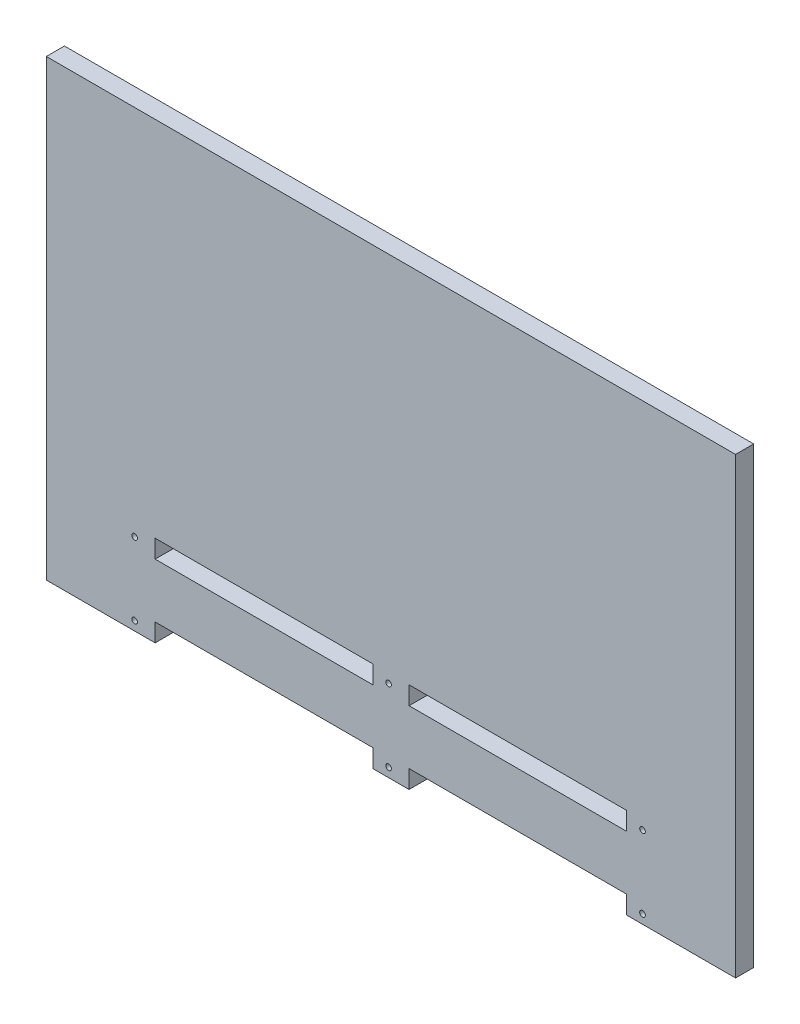
SolidWorks part; units mm, degrees
ref_plane "Ön Düzlem" through (0, 0, 0) normal (0, 0, 1) x (1, 0, 0)
ref_plane "Üst Düzlem" through (0, 0, 0) normal (0, 1, 0) x (1, 0, 0)
ref_plane "Sağ Düzlem" through (0, 0, 0) normal (1, 0, 0) x (0, 0, -1)
sketch "Çizim1" plane through (0, 0, 0) normal (0, 0, 1) x (1, 0, 0)
  line L0 (-130, -250) -> (-10, -250)
  line L1 (-150, -250) -> (150, -250)
  line L2 (-150, -250) -> (-150, 250)
  line L3 (-150, 250) -> (150, 250)
  line L4 (150, -250) -> (150, 250)
  line L5 (-150, -250) -> (150, 250) construction
  line L6 (-150, 250) -> (150, -250) construction
  line L7 (-130, -250) -> (-130, -240)
  line L8 (-10, -250) -> (-10, -240)
  line L9 (-130, -240) -> (-10, -240)
  line L10 (10, -250) -> (130, -250)
  line L11 (10, -250) -> (10, -240)
  line L12 (130, -250) -> (130, -240)
  line L13 (10, -240) -> (130, -240)
  line L14 (-130, -200) -> (-10, -200)
  line L15 (-130, -200) -> (-130, -210)
  line L16 (-10, -200) -> (-10, -210)
  line L17 (-130, -210) -> (-10, -210)
  line L18 (10, -200) -> (10, -210)
  line L19 (10, -200) -> (130, -200)
  line L20 (10, -210) -> (130, -210)
  line L21 (130, -200) -> (130, -210)
  line L22 (190, 0) -> (-190, 0)
  line L23 (-150, -250) -> (-190, -250)
  line L24 (-150, -250) -> (-150, 250)
  line L25 (-150, 250) -> (-190, 250)
  line L26 (-190, -250) -> (-190, 250)
  line L27 (150, 250) -> (190, 250)
  line L28 (150, 250) -> (150, -250)
  line L29 (150, -250) -> (190, -250)
  line L30 (190, 250) -> (190, -250)
  line L31 (190, 0) -> (190, 250)
  line L32 (-190, 0) -> (-190, 250)
  line L33 (190, 250) -> (-190, 250)
  circle A0 centre (-141.2953, -245) radius 1.55
  circle A1 centre (-1.2953, -245) radius 1.55
  circle A2 centre (138.7047, -245) radius 1.55
  circle A3 centre (-1.2953, -205) radius 1.55
  circle A4 centre (138.7047, -205) radius 1.55
  circle A5 centre (-141.2953, -205) radius 1.55
  point P0 (0, 0)
  dimension "D11" = 5
  dimension "D1" = 20
  dimension "D2" = 20
  dimension "D3" = 20
  dimension "D4" = 120
  dimension "D5" = 300
  dimension "D6" = 500
  dimension "D7" = 50
  dimension "D8" = 50
  dimension "D9" = 20
  dimension "D10" = 20
  dimension "D12" = 11.2953
  dimension "D13" = 3
  dimension "D14" = 2
extrude "Boss-Extrude2" add sketch "Çizim1" along normal blind 10 contours L26 L23 L2 L22 | L4 L22 L2 L1 L7 L9 L8 L11 L13 L12 A0 L17 L15 L14 L16 L19 L21 L20 L18 | L30 L22 L4 L29
